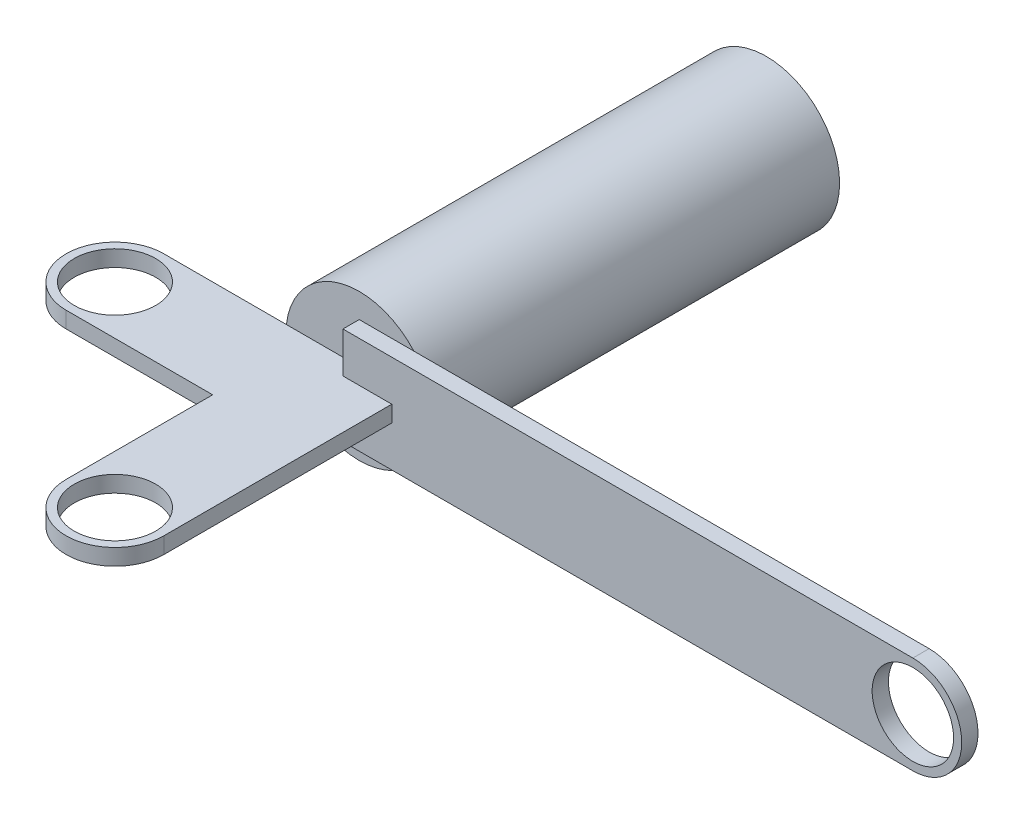
SolidWorks part; units mm, degrees
ref_plane "Front Plane" through (0, 0, 0) normal (0, 0, 1) x (1, 0, 0)
ref_plane "Top Plane" through (0, 0, 0) normal (0, 1, 0) x (1, 0, 0)
ref_plane "Right Plane" through (0, 0, 0) normal (1, 0, 0) x (0, 0, -1)
sketch "Sketch1" plane through (0, 0, 0) normal (0, 0, 1) x (1, 0, 0)
  circle A0 centre (0, 0) radius 9
  dimension "D1" = 18
extrude "Boss-Extrude1" add sketch "Sketch1" against normal blind 50
sketch "Sketch2" plane through (0, 0, 0) normal (0, 0, 1) x (1, 0, 0)
  line L0 (0, 0) -> (0, 6)
  line L1 (0, 6) -> (70, 6)
  line L2 (0, 0) -> (0, -6)
  line L3 (0, -6) -> (70, -6)
  arc A0 (70, -6) -> (70, 6) centre (70, 0) ccw
  circle A1 centre (70, 0) radius 5
  dimension "D2" = 6
  dimension "D3" = 10
  dimension "D1" = 70
extrude "Boss-Extrude2" add sketch "Sketch2" along normal blind 2 separate body
sketch "Sketch4" plane through (0, 0, 0) normal (0, 1, 0) x (1, 0, 0)
  line L1 (-6, 0) -> (6, 0)
  line L2 (-6, 0) -> (-6, -30)
  line L3 (-24, 0) -> (6, 0)
  line L4 (6, 0) -> (6, -30)
  line L6 (-24, -12) -> (6, -12)
  line L7 (6, 0) -> (6, -12)
  arc A0 (6, -30) -> (-6, -30) centre (0, -30) cw
  arc A1 (-24, 0) -> (-24, -12) centre (-24, -6) ccw
  circle A2 centre (-24, -6) radius 5
  circle A3 centre (0, -30) radius 5
  dimension "D3" = 10
  dimension "D4" = 10
  dimension "D5" = 6
  dimension "D1" = 30
  dimension "D2" = 12
  dimension "D6" = 30
extrude "Boss-Extrude3" add sketch "Sketch4" along normal mid plane 2 contours L2 L6 L4 L1 | L3 A1 L6 L2 A2 | A0 L4 L6 L2 A3
